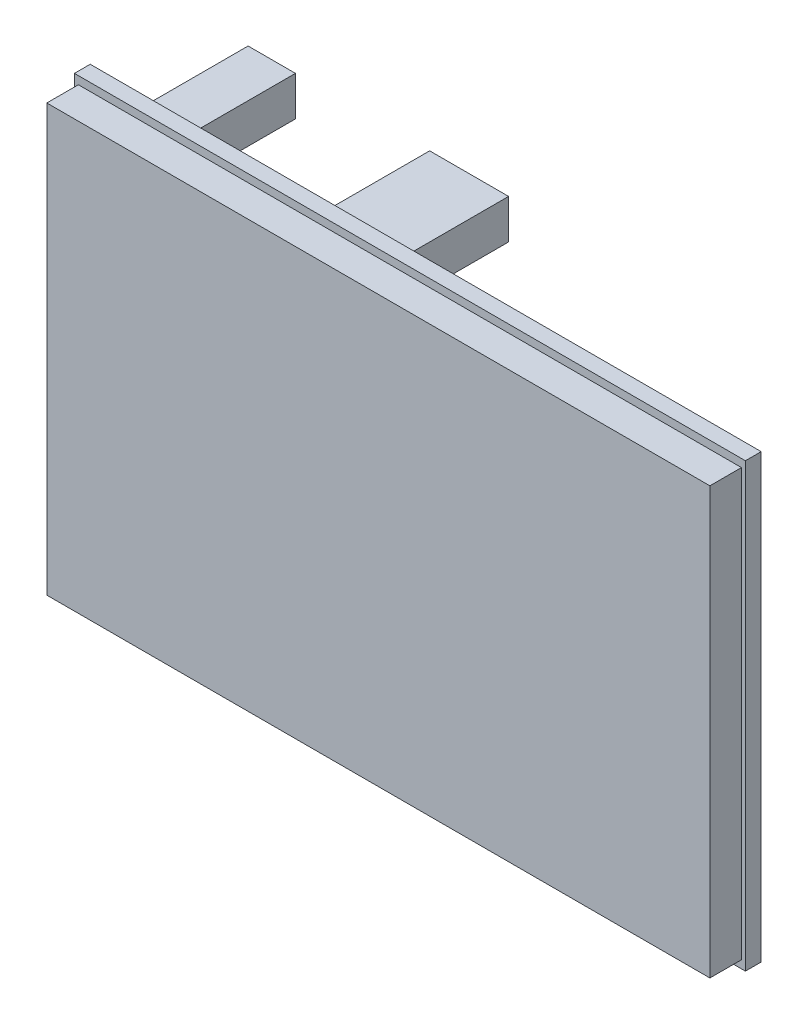
SolidWorks part; units mm, degrees
ref_plane "Plan de face" through (0, 0, 0) normal (0, 0, 1) x (1, 0, 0)
ref_plane "Plan de dessus" through (0, 0, 0) normal (0, 1, 0) x (1, 0, 0)
ref_plane "Plan de droite" through (0, 0, 0) normal (1, 0, 0) x (0, 0, -1)
sketch "Esquisse1" plane through (0, 0, 0) normal (0, 0, 1) x (1, 0, 0)
  line L1 (-42.5, 28) -> (42.5, 28)
  line L2 (-42.5, 28) -> (-42.5, -28)
  line L3 (-42.5, -28) -> (42.5, -28)
  line L4 (42.5, 28) -> (42.5, -28)
  dimension "D1" = 85
  dimension "D2" = 56
  dimension "D3" = 28
  dimension "D4" = 42.5
extrude "Boss.-Extru.1" add sketch "Esquisse1" along normal blind 2
sketch "Esquisse2" plane through (0, 0, 2) normal (0, 0, 1) x (1, 0, 0)
  line L0 (0, -1.1) -> (0, 1.1) construction
  line L1 (-42, 27) -> (42, 27)
  line L2 (-42, 27) -> (-42, -27)
  line L3 (-42, -27) -> (42, -27)
  line L4 (42, 27) -> (42, -27)
  line L5 (1.1, 0) -> (-1.1, 0) construction
  dimension "D1" = 84
  dimension "D2" = 54
  dimension "D3" = 42
  dimension "D4" = 27
extrude "Boss.-Extru.2" add sketch "Esquisse2" along normal blind 4
sketch "Esquisse3" plane through (0, 0, 0) normal (0, 0, -1) x (-1, 0, 0)
  line L0 (42.5, 28) -> (42.5, -28) construction
  line L1 (29.5, 27) -> (35.5, 27)
  line L2 (29.5, 27) -> (29.5, 22)
  line L3 (29.5, 22) -> (35.5, 22)
  line L4 (35.5, 27) -> (35.5, 22)
  line L5 (-42.5, 28) -> (42.5, 28) construction
  line L7 (2.5, 27) -> (12.5, 27)
  line L8 (2.5, 27) -> (2.5, 22)
  line L9 (2.5, 22) -> (12.5, 22)
  line L10 (12.5, 27) -> (12.5, 22)
  point P12 (12.5, 24.5)
  dimension "D1" = 6
  dimension "D2" = 5
  dimension "D3" = 7
  dimension "D4" = 1
  dimension "D5" = 10
  dimension "D6" = 5
  dimension "D7" = 1
  dimension "D8" = 30
extrude "Boss.-Extru.3" add sketch "Esquisse3" along normal blind 13
sketch "Esquisse4" plane through (0, 0, 0) normal (0, 0, -1) x (-1, 0, 0)
  line L0 (42.5, 28) -> (42.5, -28) construction
  line L1 (3.5, -19) -> (18.5, -19)
  line L2 (3.5, -19) -> (3.5, -30)
  line L3 (3.5, -30) -> (18.5, -30)
  line L4 (18.5, -19) -> (18.5, -30)
  line L5 (42.5, -28) -> (-42.5, -28) construction
  dimension "D1" = 15
  dimension "D2" = 11
  dimension "D3" = 24
  dimension "D4" = 2
extrude "Boss.-Extru.4" add sketch "Esquisse4" along normal blind 7
shell "Coque1" thickness 0.5
sketch "Esquisse5" plane through (0, 0, 0) normal (0, 0, -1) x (-1, 0, 0)
  line L0 (42.5, 28) -> (42.5, -28) construction
  line L1 (28.5, -24) -> (35.5, -24)
  line L2 (28.5, -24) -> (28.5, -29)
  line L3 (28.5, -29) -> (35.5, -29)
  line L4 (35.5, -24) -> (35.5, -29)
  line L5 (42.5, -28) -> (18.5, -28) construction
  point P8 (30.5, -28)
  dimension "D1" = 7
  dimension "D2" = 5
  dimension "D3" = 7
  dimension "D4" = 1
extrude "Boss.-Extru.5" add sketch "Esquisse5" along normal blind 3
shell "Coque2" thickness 0.2
sketch "Esquisse6" plane through (0, 0, 0) normal (0, 0, -1) x (-1, 0, 0)
  line L0 (3.5, -28) -> (-42.5, -28) construction
  line L1 (-13.5, -16) -> (-6.5, -16)
  line L2 (-13.5, -16) -> (-13.5, -28)
  line L3 (-13.5, -28) -> (-6.5, -28)
  line L4 (-6.5, -16) -> (-6.5, -28)
  line L5 (-42.5, -28) -> (-42.5, 28) construction
  dimension "D1" = 7
  dimension "D2" = 12
  dimension "D3" = 0
  dimension "D4" = 29
extrude "Boss.-Extru.6" add sketch "Esquisse6" along normal blind 4
sketch "Esquisse7" plane through (0, -28, 0) normal (0, -1, 0) x (1, 0, 0)
  line L1 (13.5, -4) -> (13.5, 0) construction
  line L2 (13.5, -4) -> (6.5, -4) construction
  circle A0 centre (10, -2) radius 2
  dimension "D1" = 4
  dimension "D2" = 3.5
  dimension "D3" = 2
extrude "Boss.-Extru.7" add sketch "Esquisse7" along normal blind 3
